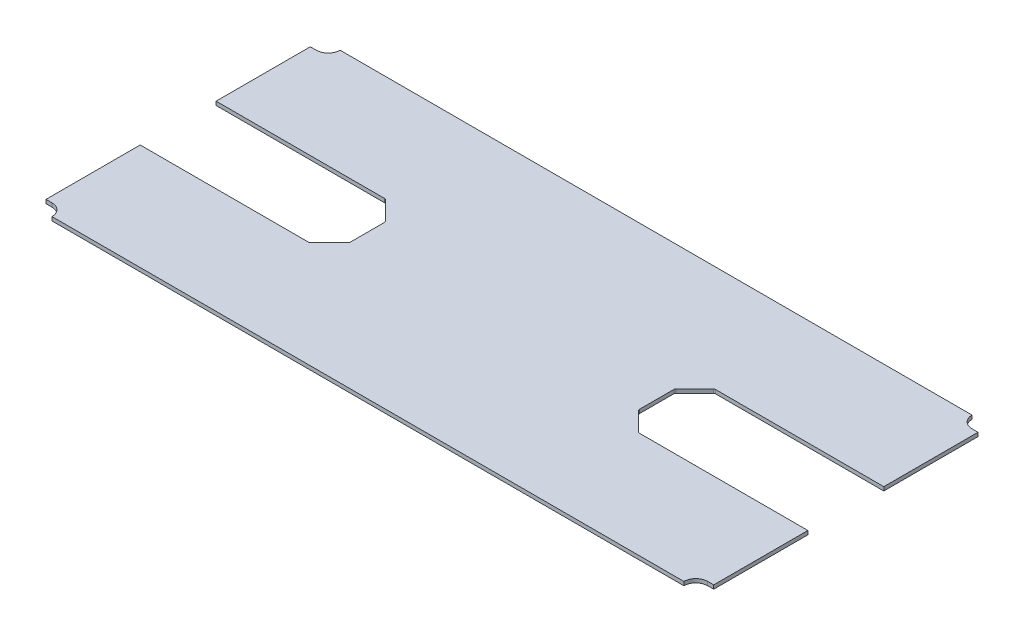
SolidWorks part; units mm, degrees
material "Mahogany"
ref_plane "Front Plane" through (0, 0, 0) normal (0, 0, 1) x (1, 0, 0)
ref_plane "Top Plane" through (0, 0, 0) normal (0, 1, 0) x (1, 0, 0)
ref_plane "Right Plane" through (0, 0, 0) normal (1, 0, 0) x (0, 0, -1)
sketch "Sketch1" plane through (0, 0, 0) normal (0, 1, 0) x (1, 0, 0)
  line L0 (-840, 95.5) -> (-364, 95.5)
  line L1 (-840, 362.5) -> (840, 362.5)
  line L2 (-840, 362.5) -> (-840, -362.5)
  line L3 (-840, -362.5) -> (840, -362.5)
  line L4 (840, 362.5) -> (840, -362.5)
  line L5 (-840, 362.5) -> (840, -362.5) construction
  line L6 (-840, -362.5) -> (840, 362.5) construction
  line L23 (-364, 95.5) -> (-364, -95.5)
  line L24 (-364, -95.5) -> (-840, -95.5)
  line L25 (840, 95.5) -> (364, 95.5)
  line L26 (364, 95.5) -> (364, -95.5)
  line L27 (364, -95.5) -> (840, -95.5)
  line L28 (-840, 332.5) -> (-825, 332.5)
  line L29 (0, -362.5) -> (0, 362.5) construction
  line L30 (-840, 0) -> (840, 0) construction
  line L31 (-840, -332.5) -> (-825, -332.5)
  line L32 (840, 332.5) -> (825, 332.5)
  line L33 (840, -332.5) -> (825, -332.5)
  arc A0 (-825, 332.5) -> (-795, 362.5) centre (-825, 362.5) ccw
  arc A1 (-825, -332.5) -> (-795, -362.5) centre (-825, -362.5) cw
  arc A2 (825, 332.5) -> (795, 362.5) centre (825, 362.5) cw
  arc A3 (825, -332.5) -> (795, -362.5) centre (825, -362.5) ccw
  point P0 (0, 0)
  point P26 (364, 0)
  point P27 (-364, 0)
  dimension "D6" = 30
  dimension "D4" = 476
  dimension "D5" = 191
  dimension "D2" = 725
  dimension "D1" = 1680
  dimension "D3" = 15
extrude "Boss-Extrude1" add sketch "Sketch1" along normal blind 9.525
chamfer "Chamfer1" distance 50 angle 45 4 edges at (364, 4.7625, 95.5) (364, 4.7625, -95.5) (-364, 4.7625, 95.5) (-364, 4.7625, -95.5)
fillet "Fillet2" radius 5 8 edges at (364, 4.7625, -45.5) (364, 4.7625, 45.5) (414, 4.7625, 95.5) (414, 4.7625, -95.5) (-414, 4.7625, 95.5) (-364, 4.7625, 45.5) (-364, 4.7625, -45.5) (-414, 4.7625, -95.5)
equation "\"W\"= 1700"
equation "\"L\"= 760"
equation "\"H\"= 810"
equation "\"ARM_BOLT_SPACING\"= 166"
equation "\"ARM_TO_WALL\"= 300"
equation "\"D4@Sketch1\"=\"ARM_TO_WALL\"+\"ARM_BOLT_SPACING\"+10"
equation "\"D5@Sketch1\"=\"ARM_BOLT_SPACING\"+25"
equation "\"D2@Sketch1\"=\"L\"-35"
equation "\"D1@Sketch1\"=\"W\"-20"
